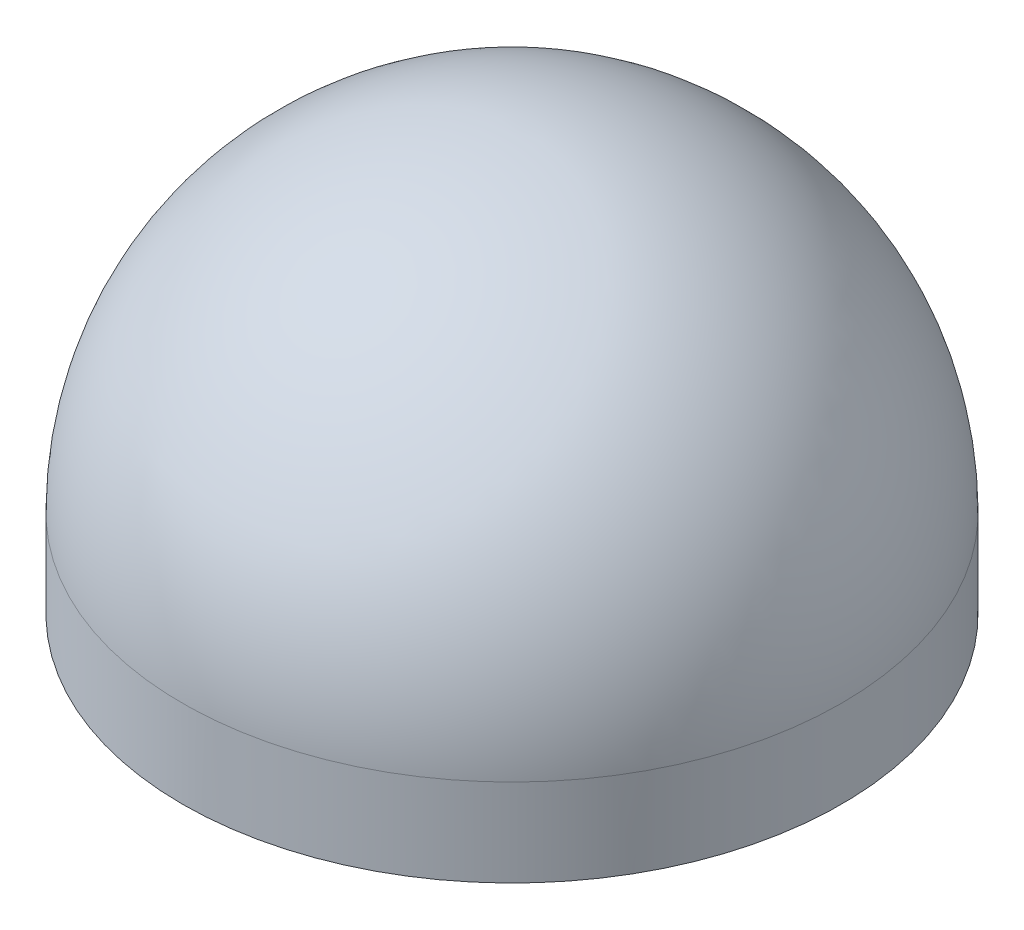
SolidWorks part; units mm, degrees
ref_plane "Front Plane" through (0, 0, 0) normal (0, 0, 1) x (1, 0, 0)
ref_plane "Top Plane" through (0, 0, 0) normal (0, 1, 0) x (1, 0, 0)
ref_plane "Right Plane" through (0, 0, 0) normal (1, 0, 0) x (0, 0, -1)
sketch "Sketch1" plane through (0, 0, 0) normal (0, 0, 1) x (1, 0, 0)
  line L0 (0, 0) -> (0, 65.3751) construction
  line L1 (-1.5875, 0) -> (-22.225, 0)
  line L2 (-22.225, 0) -> (-22.225, 5.8966)
  line L3 (-1.5875, 2.1082) -> (-1.5875, 6.35)
  line L4 (-1.5875, 0) -> (-1.5875, 2.1082)
  line L5 (-6.35, 2.1082) -> (-21.1836, 2.1082)
  line L6 (-21.1836, 2.1082) -> (-21.1836, 3.7621)
  line L7 (-21.1836, 3.7621) -> (-6.35, 24.9466)
  line L8 (-6.35, 24.9466) -> (0, 24.9466)
  line L9 (0, 24.9466) -> (0, 28.1216)
  line L10 (-1.5875, 6.35) -> (-6.35, 6.35)
  line L11 (-6.35, 6.35) -> (-6.35, 2.1082)
  arc A0 (-22.225, 5.8966) -> (0, 28.1216) centre (0, 5.8966) cw
  dimension "D1" = 35
  dimension "D2" = 3.175
  dimension "D3" = 1.0414
  dimension "D4" = 2.1082
  dimension "D5" = 12.7
  dimension "D6" = 44.45
  dimension "D7" = 12.7
  dimension "D8" = 6.35
  dimension "D9" = 3.175
revolve "Revolve1" add sketch "Sketch1" angle 360 about L0
